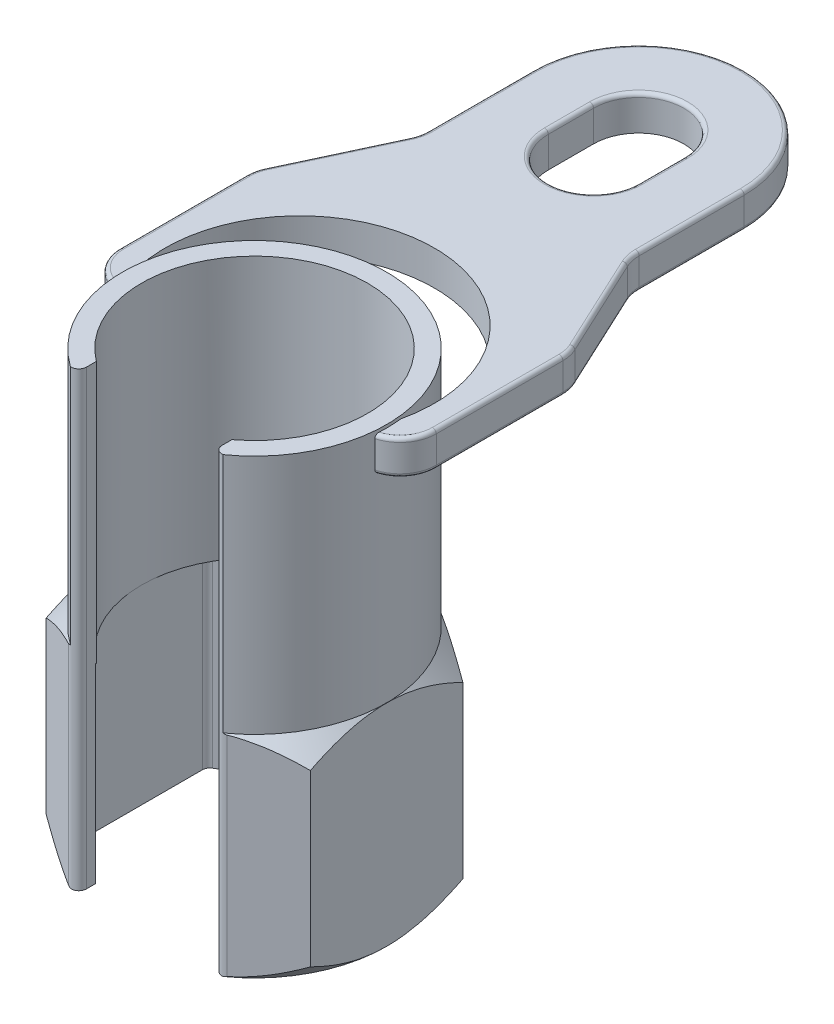
SolidWorks part; units mm, degrees
ref_plane "Front" through (0, 0, 0) normal (0, 0, 1) x (1, 0, 0)
ref_plane "Top" through (0, 0, 0) normal (0, 1, 0) x (1, 0, 0)
ref_plane "Right" through (0, 0, 0) normal (1, 0, 0) x (0, 0, -1)
sketch "Sketch1" plane through (0, 0, 0) normal (0, 1, 0) x (1, 0, 0)
  line L0 (-9, -12) -> (-9, -15.0538)
  line L1 (0, 20.25) -> (-17.537, 10.125)
  line L2 (0, 11.9615) -> (0, -7.933) construction
  line L3 (-17.537, 10.125) -> (-17.537, -10.125)
  line L4 (-17.537, -10.125) -> (-9, -15.0538)
  line L5 (9, -15.0538) -> (17.537, -10.125)
  line L6 (17.537, -10.125) -> (17.537, 10.125)
  line L7 (17.537, 10.125) -> (0, 20.25)
  line L8 (9, -12) -> (9, -15.0538)
  arc A0 (9, -15.0515) -> (-9, -15.0515) centre (0, 0) ccw construction
  arc A1 (9, -12) -> (-9, -12) centre (0, 0) ccw
  point P18 (-17.537, -10.125)
  point P26 (17.537, 10.125)
  dimension "D" = 40.5
  dimension "D2" = 30
  dimension "C" = 18
extrude "Extrude1" add sketch "Sketch1" along normal blind 28
sketch "Sketch3" plane through (0, 28, 0) normal (0, 1, 0) x (-1, 0, 0)
  line L0 (-17.537, 10.125) -> (-17.537, -10.125) construction
  line L2 (-9, 15.0514) -> (-9, 12)
  line L3 (9, 15.0514) -> (9, 12)
  arc A0 (-9, 12) -> (9, 12) centre (0, 0) ccw
  arc A1 (-9, 12) -> (9, 12) centre (0, 0) ccw construction
  arc A2 (-9, 15.0514) -> (9, 15.0514) centre (0, 0) ccw
  dimension "D1" = 0.0001
extrude "Extrude2" add sketch "Sketch3" along normal blind 32
sketch "Sketch8" plane through (0, 0, 0) normal (0, -1, 0) x (1, 0, 0)
  line L1 (17.537, 10.125) -> (17.537, -10.125) construction
  circle A0 centre (0, 0) radius 17.537
extrude "Cut-Extrude4" cut sketch "Sketch8" against normal through all draft 45 flip side to cut
sketch "Sketch19" plane through (0, 28, 0) normal (0, 1, 0) x (-1, 0, 0)
  circle A1 centre (0, 0) radius 17.5369
  arc A2 (-9, 15.0514) -> (9, 15.0514) centre (0, 0) ccw construction
extrude "Cut-Extrude6" cut sketch "Sketch19" against normal through all draft 45 flip side to cut
sketch "Sketch26" plane through (0, 0, 0) normal (0, -1, 0) x (1, 0, 0)
  line L1 (-15, -8.6603) -> (0, -17.3205)
  line L2 (0, -17.3205) -> (15, -8.6603)
  line L3 (15, -8.6603) -> (15, 8.6603)
  line L4 (15, 8.6603) -> (0, 17.3205)
  line L5 (0, 17.3205) -> (-15, 8.6603)
  line L6 (-15, 8.6603) -> (-15, -8.6603)
  circle A0 centre (0, 0) radius 15 construction
  dimension "D1" = 30
extrude "Cut-Extrude9" cut sketch "Sketch26" against normal up to vertex (38.5 mm away)
fillet "Fillet1" radius 1 7 edges at (-15, 12.6435, -8.6603) (-15, 12.6435, 8.6603) (15, 12.6435, 8.6603) (15, 12.6435, -8.6603) (-9, 14, 15.0538) (9, 14, 15.0538) (0, 12.6435, -17.3205)
sketch "Sketch4" [suppressed] plane through (0, 0, 0) normal (0, 1, 0) x (-1, 0, 0)
  line L0 (0, -11.2014) -> (0, 12.8888) construction
  line L1 (-10, -2.5) -> (10, -2.5)
  line L2 (-10, -2.5) -> (-10, 3.8)
  line L3 (-10, 3.8) -> (10, 3.8)
  line L4 (10, -2.5) -> (10, 3.8)
  line L5 (16.2585, 0) -> (-21.4153, 0) construction
  dimension "D1" = 30
  dimension "D2" = 5.5
  dimension "D3" = 4.2
sketch "Sketch12" [suppressed] plane through (0, 0, 0) normal (0, 1, 0) x (1, 0, 0)
  line L0 (-11, -4) -> (11, -4)
  line L1 (0, 0) -> (-11.4274, 0) construction
  line L2 (-11, 2.7) -> (11, 2.7)
  line L3 (-4.5, 14.3091) -> (4.5, 14.3091)
  line L4 (-7, 3.2909) -> (-7, -3.2909) construction
  line L5 (7, -3.2909) -> (7, 3.2909) construction
  arc A0 (-11, -4) -> (11, -4) centre (0, 0) ccw
  arc A1 (-6.3246, -3) -> (6.3246, -3) centre (0, 0) ccw construction
  arc A2 (-4.5, 14.3091) -> (-11, 2.7) centre (2.617, 2.7) ccw
  arc A3 (-4.5, 14.3091) -> (4.5, 14.3091) centre (0, 0) ccw construction
  arc A4 (4.5, 14.3091) -> (11, 2.7) centre (-2.617, 2.7) cw
ref_plane "Plane3" through (0, 55, 0) normal (0, 1, 0) x (-1, 0, 0)
sketch "Sketch16" plane through (0, 55, 0) normal (0, 1, 0) x (-1, 0, 0)
  line L5 (0, 0) -> (0, 54.2988) construction
  line L6 (-14, -51) -> (-14, -37.0649)
  line L10 (14, -37.0649) -> (14, -51)
  line L11 (20.5497, -21.965) -> (14.4503, -35.035)
  line L12 (-20.5497, -21.965) -> (-14.4503, -35.035)
  line L13 (-21, -3.1282) -> (-21, -19.9351)
  line L14 (21, -3.1282) -> (21, -19.9351)
  line L15 (38.3763, 1.5) -> (-38.1367, 1.5) construction
  arc A0 (-10.1334, 14.3129) -> (10.1334, 14.3129) centre (0, 0) ccw construction
  arc A1 (-17.4726, 1.5) -> (17.4726, 1.5) centre (0, 0) ccw
  arc A2 (21, -3.1282) -> (17.4726, 1.5) centre (16.2, -3.1282) ccw
  arc A3 (-21, -3.1282) -> (-17.4726, 1.5) centre (-16.2, -3.1282) cw
  arc A4 (-21, -19.9351) -> (-20.5497, -21.965) centre (-16.2, -19.9351) ccw
  arc A5 (-14.4503, -35.035) -> (-14, -37.0649) centre (-18.8, -37.0649) cw
  arc A7 (21, -19.9351) -> (20.5497, -21.965) centre (16.2, -19.9351) cw
  arc A8 (14.4503, -35.035) -> (14, -37.0649) centre (18.8, -37.0649) ccw
  arc A15 (14, -51) -> (-14, -51) centre (0, -51) cw
  point P18 (-21, -21)
  point P22 (-14, -36)
  point P25 (21, -21)
  point P30 (14, -36)
  dimension "D1" = 42
  dimension "D2" = 21
  dimension "D3" = 36
  dimension "D4" = 4.8
  dimension "D6" = 28
  dimension "D7" = 51
  dimension "D14" = 1.5
extrude "Extrude7" add sketch "Sketch16" along normal blind 4.6
sketch "Sketch25" plane through (0, 59.6, 0) normal (0, -1, 0) x (1, 0, 0)
  line L1 (-29.4486, 0) -> (37.9585, 0) construction
  line L3 (0, -57.3769) -> (0, 10.8445) construction
  line L4 (-6, -51) -> (-6, -45)
  line L5 (6, -51) -> (6, -45)
  arc A0 (-10.1334, 14.3129) -> (10.1334, 14.3129) centre (0, 0) ccw construction
  arc A2 (-14, -51) -> (14, -51) centre (0, -51) ccw construction
  arc A6 (17.4225, -2) -> (-17.4225, -2) centre (0, 0) cw
  arc A7 (17.4225, -2) -> (-17.4225, -2) centre (0, -6) cw
  arc A8 (6, -51) -> (-6, -51) centre (0, -51) cw
  arc A9 (6, -45) -> (-6, -45) centre (0, -45) ccw
  dimension "D1" = 20
  dimension "D2" = 12
  dimension "D3" = 2
  dimension "D4" = 6
extrude "Cut-Extrude8" cut sketch "Sketch25" along normal up to next
fillet "Fillet4" radius 0.5 30 edges at (6, 59.6, -48) (0, 59.6, -57) (-6, 59.6, -48) (20.0176, 59.6, -0.2186) (21, 59.6, -11.5317) (20.8861, 59.6, -20.9747) (-20.0176, 59.6, -0.2186) (-21, 59.6, -11.5317) (-20.8861, 59.6, -20.9747) (-17.5, 59.6, -28.5) (-14.1139, 59.6, -36.0253) (-14, 59.6, -44.0324) (0, 59.6, -65) (14, 59.6, -44.0324) (14.1139, 59.6, -36.0253) (20.0176, 55, -0.2186) (21, 55, -11.5317) (20.8861, 55, -20.9747) (-20.0176, 55, -0.2186) (-21, 55, -11.5317) (-20.8861, 55, -20.9747) (-17.5, 55, -28.5) (-14.1139, 55, -36.0253) (-14, 55, -44.0324) (0, 55, -65) (14, 55, -44.0324) (14.1139, 55, -36.0253) (0, 59.6, -39) (17.5, 59.6, -28.5) (17.5, 55, -28.5)
sketch "Sketch20" [suppressed] plane through (0, 0, 0) normal (0, 1, 0) x (1, 0, 0)
  line L0 (0, 0) -> (0, 12.8849) construction
  line L1 (-7.5, -9.3675) -> (-7.5, -14.4157)
  line L2 (7.5, -9.3675) -> (7.5, -14.4157)
  arc A0 (7.5, -14.4157) -> (-7.5, -14.4157) centre (0, 0) ccw
  arc A1 (7.5, -9.3675) -> (-7.5, -9.3675) centre (0, 0) ccw
  circle A2 centre (0, 0) radius 16.25 construction
  circle A3 centre (0, 0) radius 12 construction
  dimension "D1" = 40.5
  dimension "D2" = 30
  dimension "D3" = 18
extrude "Extrude3" [suppressed] add sketch "Sketch20" along normal blind 46
ref_plane "Plane7" [suppressed] through (0, 41.999, 0) normal (0, 1, 0) x (-1, 0, 0)
sketch "Sketch21" [suppressed] plane through (0, 41.999, 0) normal (0, 1, 0) x (-1, 0, 0)
  line L1 (2.5, 16.0565) -> (2.5, 19.8734)
  line L2 (7.5, 14.4157) -> (7.5, 9.3675) construction
  line L4 (7.5, 14.4157) -> (7.5, 18.5729)
  arc A1 (2.5, 16.0565) -> (7.5, 14.4157) centre (0, 0) ccw
  arc A2 (2.5, 19.8734) -> (7.5, 18.5729) centre (0, 0) ccw
  arc A3 (-7.5, 14.4157) -> (7.5, 14.4157) centre (0, 0) ccw construction
  dimension "D1" = 4.14
  dimension "D2" = 2.5
extrude "Extrude4" [suppressed] add sketch "Sketch21" against normal blind 14 separate body
ref_plane "Plane6" [suppressed] through (5.0421, 41.999, -19.385) normal (0.2517, 0, -0.9678) x (-0.9678, 0, -0.2517)
sketch "Sketch22" [suppressed] plane through (5.0421, 41.999, -19.385) normal (0.2517, 0, -0.9678) x (-0.9678, 0, -0.2517)
  line L0 (20.03, 0) -> (-20.03, 0) construction
  line L1 (0, 0) -> (0, 14.8678) construction
  line L2 (-3.2, -3.3) -> (3.2, -3.3)
  line L3 (-3.2, -3.3) -> (-3.2, -9.7)
  line L4 (-3.2, -9.7) -> (3.2, -9.7)
  line L5 (3.2, -3.3) -> (3.2, -9.7)
  line L7 (-18.9345, -6.5) -> (19.4735, -6.5) construction
  dimension "D1" = 7.2
  dimension "D2" = 7
  dimension "D3" = 7.2
extrude "Extrude5" [suppressed] add sketch "Sketch22" along normal blind 14 and the other way up to next
sketch "Sketch23" [suppressed] plane through (8.0628, 0, -30.9986) normal (0.2517, 0, -0.9678) x (-0.9678, 0, -0.2517)
  circle A0 centre (0, 35.499) radius 4.5255
extrude "Extrude6" [suppressed] add sketch "Sketch23" along normal blind 36 draft 2
dome "Dome1" [suppressed] faces to dome 1 distance 3 parameters "D1"=3
sketch "Sketch24" [suppressed] plane through (0, 0, 0) normal (0, -1, 0) x (1, 0, 0)
  line L2 (-12, 6.9282) -> (-12, -6.9282)
  line L3 (-12, -6.9282) -> (0, -13.8564)
  line L4 (0, -13.8564) -> (12, -6.9282)
  line L5 (12, -6.9282) -> (12, 6.9282)
  line L6 (12, 6.9282) -> (0, 13.8564)
  line L7 (0, 13.8564) -> (-12, 6.9282)
  circle A0 centre (0, 0) radius 12 construction
  dimension "D1" = 30
extrude "Cut-Extrude7" [suppressed] cut sketch "Sketch24" against normal through all
fillet "Fillet2" [suppressed] radius 0.5
fillet "Fillet3" [suppressed] radius 0.5
fillet "Fillet5" [suppressed] radius 1
